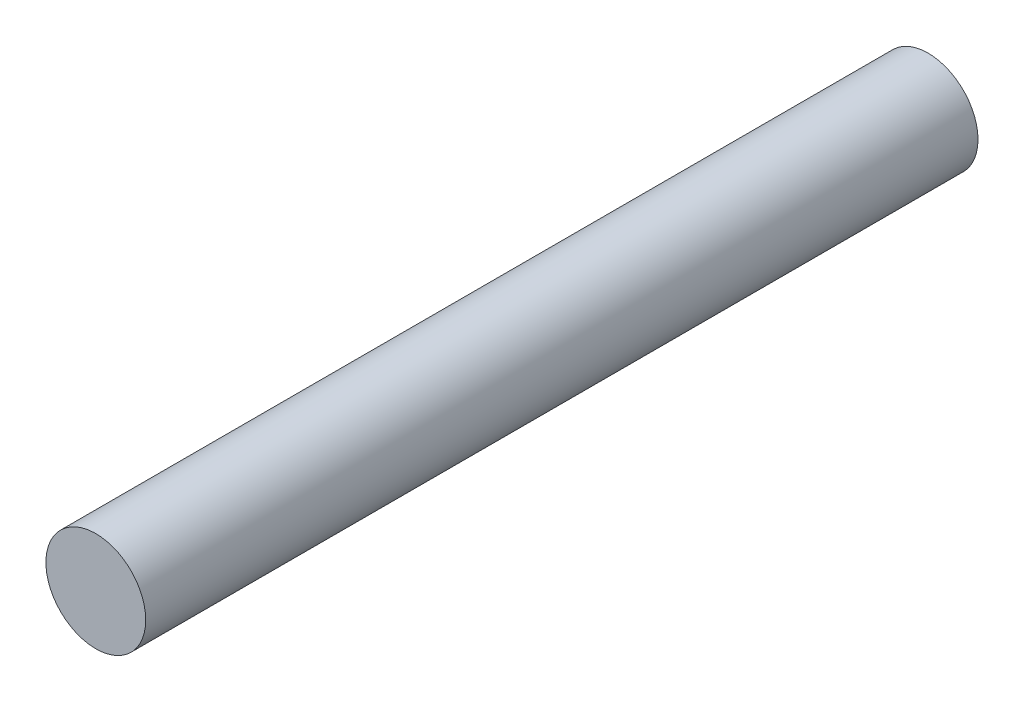
SolidWorks part; units mm, degrees
ref_plane "Front Plane" through (0, 0, 0) normal (0, 0, 1) x (1, 0, 0)
ref_plane "Top Plane" through (0, 0, 0) normal (0, 1, 0) x (1, 0, 0)
ref_plane "Right Plane" through (0, 0, 0) normal (1, 0, 0) x (0, 0, -1)
sketch "Sketch1" plane through (0, 0, 0) normal (0, 0, 1) x (1, 0, 0)
  circle A0 centre (0, 0) radius 3
  dimension "D1" = 6
extrude "Boss-Extrude1" add sketch "Sketch1" along normal blind 50.038
